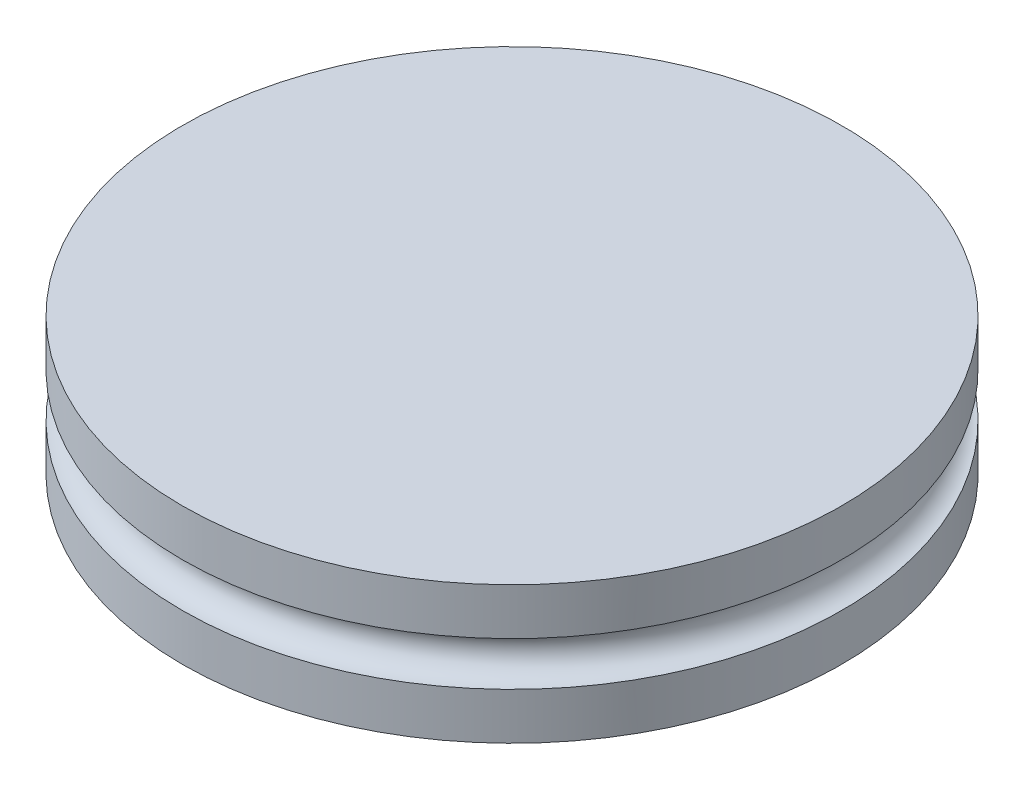
SolidWorks part; units mm, degrees
ref_plane "Front Plane" through (0, 0, 0) normal (0, 0, 1) x (1, 0, 0)
ref_plane "Top Plane" through (0, 0, 0) normal (0, 1, 0) x (1, 0, 0)
ref_plane "Right Plane" through (0, 0, 0) normal (1, 0, 0) x (0, 0, -1)
sketch "Sketch1" plane through (0, 0, 0) normal (0, 1, 0) x (1, 0, 0)
  circle A0 centre (0, 0) radius 7.62
extrude "Boss-Extrude1" add sketch "Sketch1" along normal blind 3.175
sketch "Sketch3" plane through (0, 0, 0) normal (0, 0, 1) x (1, 0, 0)
  line L0 (7.62, 3.175) -> (-7.62, 3.175) construction
  line L1 (-7.62, 3.175) -> (-7.62, 0) construction
  circle A0 centre (-6.604, 1.5875) radius 0.508
  dimension "D1" = 1.5875
  dimension "D2" = 1.016
extrude "Cut-Extrude1" cut sketch "Sketch3" against normal mid plane 50.8
sketch "Sketch4" plane through (0, 0, 0) normal (0, 0, 1) x (1, 0, 0)
  line L0 (7.62, 0) -> (7.62, 3.175) construction
  circle A0 centre (7.62, 1.5875) radius 0.508
sketch "Sketch5" plane through (0, 0, 0) normal (0, 1, 0) x (1, 0, 0)
  line L0 (0, 0) -> (-7.5548, -0.9946) construction
  line L1 (0, 0) -> (-7.5548, 0.9946) construction
  line L2 (0, 0) -> (-7.62, 0) construction
  arc A0 (-7.5548, -0.9946) -> (-7.5548, 0.9946) centre (0, 0) ccw
  dimension "D1" = 15
  dimension "D2" = 7.5
ref_plane "Plane1" through (0, 0, -7.62) normal (0, 0, 1) x (1, 0, 0)
ref_plane "Plane2" through (0, 0, 7.62) normal (0, 0, 1) x (1, 0, 0)
sketch "Sketch6" plane through (0, 0, -7.62) normal (0, 0, 1) x (1, 0, 0)
  line L1 (-6.604, 2.0955) -> (-7.8245, 2.0955)
  line L2 (-6.604, 2.0955) -> (-6.604, 1.0795)
  line L3 (-6.604, 1.0795) -> (-7.8245, 1.0795)
  line L4 (-7.8245, 2.0955) -> (-7.8245, 1.0795)
  circle A0 centre (-6.604, 1.5875) radius 0.508 construction
  point P8 (0, 0)
  point P9 (-6.6396, 2.0942)
  point P10 (0, 0)
  dimension "D1" = 1.016
extrude "Cut-Extrude2" cut sketch "Sketch6" along normal blind 7.366
sketch "Sketch7" plane through (0, 0, 7.62) normal (0, 0, 1) x (1, 0, 0)
  line L1 (-6.604, 2.0955) -> (-7.8245, 2.0955)
  line L2 (-6.604, 2.0955) -> (-6.604, 1.0795)
  line L3 (-6.604, 1.0795) -> (-7.8245, 1.0795)
  line L4 (-7.8245, 2.0955) -> (-7.8245, 1.0795)
  circle A0 centre (-6.604, 1.5875) radius 0.508 construction
  arc A1 (-6.604, 2.0955) -> (-6.604, 1.0795) centre (-6.604, 1.5875) ccw construction
  point P8 (-7.112, 1.778)
  point P9 (0, 0)
  dimension "D1" = 1.016
extrude "Cut-Extrude3" cut sketch "Sketch7" against normal blind 7.366
sweep "Cut-Sweep1" cut profiles "Sketch4" path "Sketch5"
